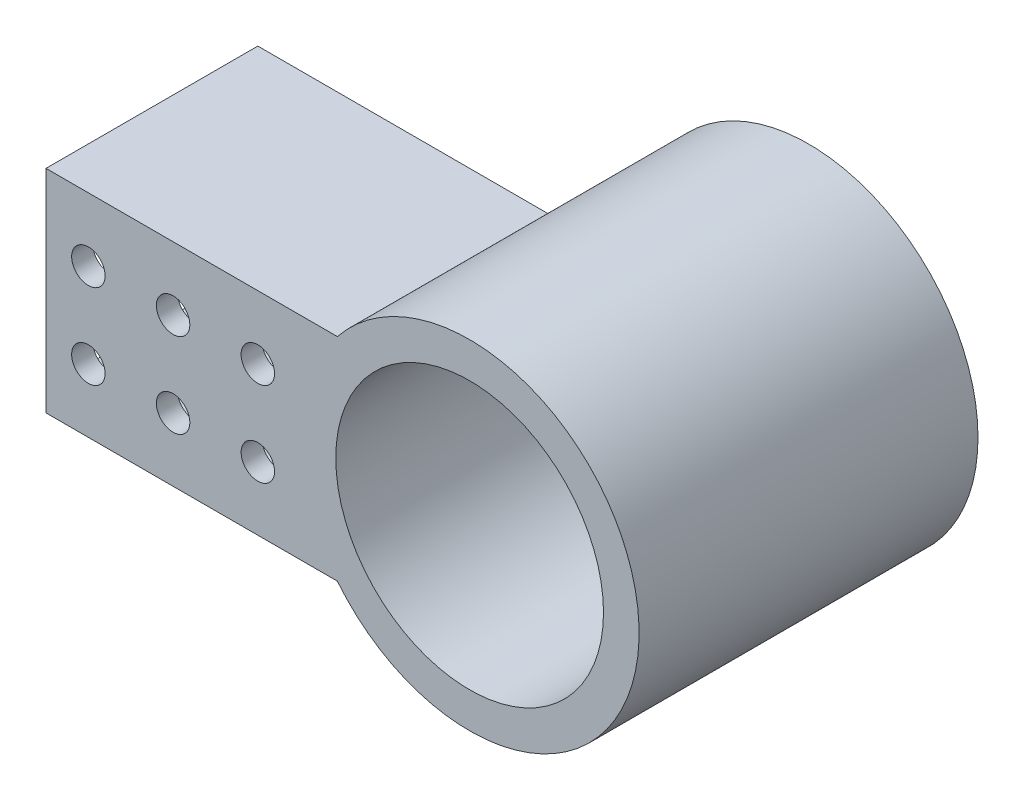
SolidWorks part; units mm, degrees
material "6061-T6 (SS)"
ref_plane "Front Plane" through (0, 0, 0) normal (0, 0, 1) x (1, 0, 0)
ref_plane "Top Plane" through (0, 0, 0) normal (0, 1, 0) x (1, 0, 0)
ref_plane "Right Plane" through (0, 0, 0) normal (1, 0, 0) x (0, 0, -1)
sketch "Sketch1" plane through (0, 0, 0) normal (0, 0, 1) x (1, 0, 0)
  line L0 (0, 0) -> (-25.4, 0) construction
  line L5 (-25.4, 0) -> (25.4, 0) construction
  circle A0 centre (0, 0) radius 25.4
  circle A1 centre (0, 0) radius 20.066
  dimension "D1" = 40.132
  dimension "D2" = 50.8
extrude "Boss-Extrude1" add sketch "Sketch1" along normal blind 50.8
sketch "Sketch2" plane through (0, 0, 50.8) normal (0, 0, 1) x (1, 0, 0)
  line L1 (-19.8279, 15.875) -> (-63.5, 15.875)
  line L3 (-19.8279, -15.875) -> (-63.5, -15.875)
  line L4 (-63.5, 15.875) -> (-63.5, -15.875)
  circle A0 centre (0, 0) radius 25.4 construction
  circle A2 centre (0, 0) radius 25.4
  arc A3 (-19.8279, 15.875) -> (-19.8279, -15.875) centre (0, 0) ccw
  point P8 (-25.4, 0)
  dimension "D4" = 0
  dimension "D1" = 31.75
  dimension "D2" = 15.875
  dimension "D3" = 38.1
extrude "Boss-Extrude2" add sketch "Sketch2" against normal blind 31.75
sketch "Sketch3" plane through (-63.5, 0, 0) normal (-1, 0, 0) x (0, 0, 1)
  line L0 (50.8, 15.875) -> (50.8, -15.875) construction
  line L1 (22.225, 12.7) -> (47.625, 12.7)
  line L2 (22.225, 12.7) -> (22.225, -12.7)
  line L3 (22.225, -12.7) -> (47.625, -12.7)
  line L4 (47.625, 12.7) -> (47.625, -12.7)
  line L5 (19.05, -15.875) -> (50.8, -15.875) construction
  dimension "D1" = 25.4
  dimension "D2" = 25.4
  dimension "D3" = 3.175
  dimension "D4" = 3.175
extrude "Cut-Extrude1" cut sketch "Sketch3" against normal blind 38.1
sketch "Sketch4" plane through (0, 0, 50.8) normal (0, 0, 1) x (1, 0, 0)
  line L0 (-63.5, 15.875) -> (-63.5, -15.875) construction
  circle A0 centre (-57.15, 6.35) radius 2.5083
  circle A1 centre (-57.15, -6.35) radius 2.5083
  point P8 (-63.5, 0)
  dimension "D1" = 5.0165
  dimension "D2" = 5.0165
  dimension "D3" = 6.35
  dimension "D4" = 6.35
  dimension "D5" = 6.35
  dimension "D6" = 6.35
extrude "Cut-Extrude2" cut sketch "Sketch4" against normal blind 31.75
pattern_linear "LPattern1" count 3 spacing 12.7 along (1, 0, 0) of "Cut-Extrude2"
